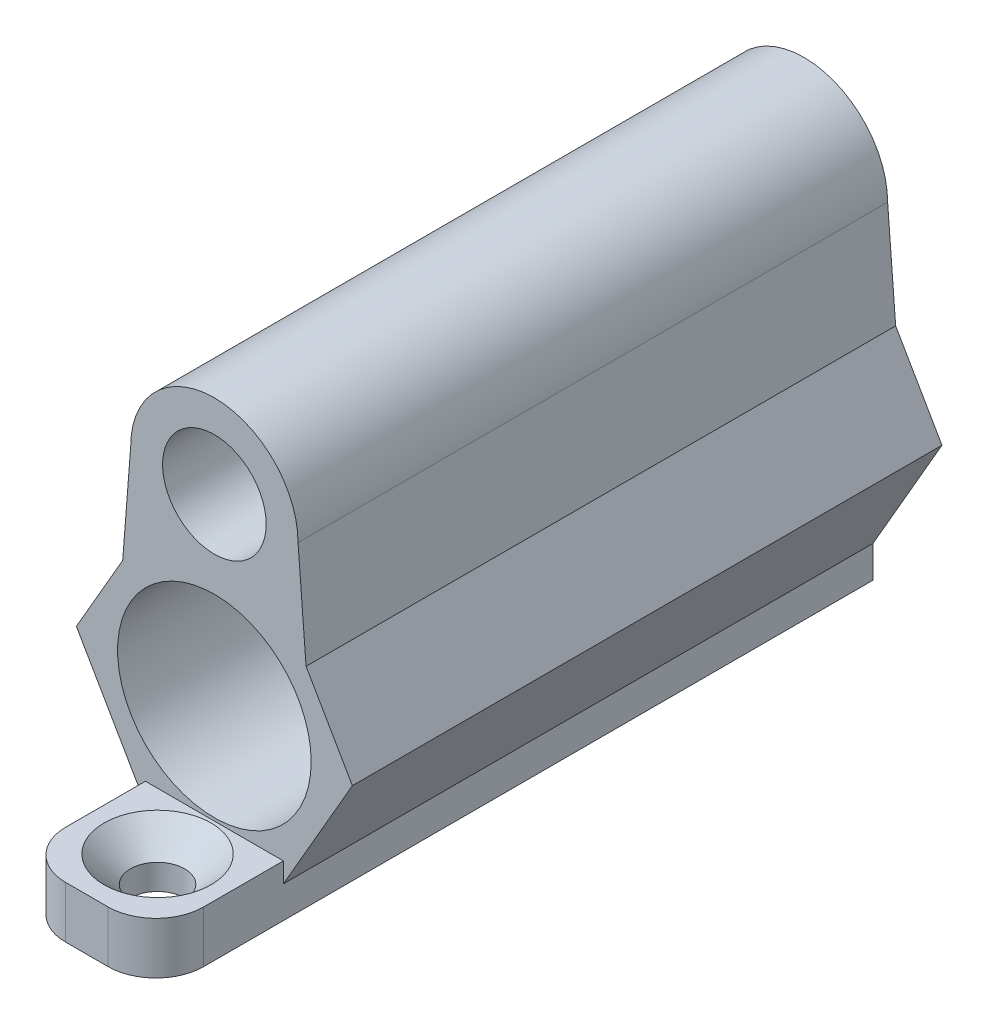
SolidWorks part; units mm, degrees
ref_plane "Front Plane" through (0, 0, 0) normal (0, 0, 1) x (1, 0, 0)
ref_plane "Top Plane" through (0, 0, 0) normal (0, 1, 0) x (1, 0, 0)
ref_plane "Right Plane" through (0, 0, 0) normal (1, 0, 0) x (0, 0, -1)
sketch "Sketch1" plane through (0, 0, 0) normal (0, 0, 1) x (1, 0, 0)
  line L0 (0, 0) -> (0, 43.6394) construction
  line L1 (0, 0) -> (58.8583, 0) construction
  line L2 (0, 0) -> (0, -43.088) construction
  line L3 (-3.9875, 4.3165) -> (-4.3301, 0)
  line L4 (8.6603, -7.5) -> (4.3301, 0)
  line L5 (4.3301, 0) -> (-4.3301, 0)
  line L6 (-4.3301, 0) -> (-8.6603, -7.5)
  line L7 (-8.6603, -7.5) -> (-4.3301, -15)
  line L8 (-4.3301, -15) -> (4.3301, -15)
  line L9 (4.3301, -15) -> (8.6603, -7.5)
  line L10 (3.9875, 4.3165) -> (4.3301, 0)
  circle A0 centre (0, -7.5) radius 7.5 construction
  circle A1 centre (0, 4) radius 4
  circle A2 centre (0, 4) radius 2.44
  circle A3 centre (0, -7.5) radius 2.44
  dimension "D1" = 15
  dimension "D2" = 8
  dimension "D3" = 4.88
  dimension "D4" = 4.88
extrude "Boss-Extrude2" add sketch "Sketch1" along normal blind 37 contours L8 L9 L4 L5 L6 L7 A3 | A1 L3 L5 | A1 A2 | A1 L5 L10
sketch "Sketch8" plane through (0, 0, 37) normal (0, 0, 1) x (1, 0, 0)
  circle A0 centre (0, 4) radius 3.25
  circle A1 centre (0, -7.5) radius 6.075
extrude "Cut-Extrude1" cut sketch "Sketch8" against normal blind 33
sketch "Sketch9" plane through (0, 0, 37) normal (0, 0, 1) x (1, 0, 0)
  line L1 (-4.3301, -15) -> (4.3301, -15)
  line L2 (-4.3301, -15) -> (-4.3301, -13.7541)
  line L3 (-4.3301, -13.7541) -> (4.3301, -13.7541)
  line L4 (4.3301, -15) -> (4.3301, -13.7541)
  dimension "D1" = 1.2459
sketch "Sketch15" plane through (0, 0, 37) normal (0, 0, 1) x (1, 0, 0)
  line L1 (-5.25, 4) -> (-5.7535, -2.4653)
  line L2 (-4.3301, 0) -> (-8.6603, -7.5) construction
  line L3 (5.25, 4) -> (5.7535, -2.4653)
  line L4 (8.6603, -7.5) -> (4.3301, 0) construction
  line L5 (5.7535, -2.4653) -> (2.1457, -0.7915)
  line L6 (-5.7535, -2.4653) -> (-1.8843, -0.9002)
  circle A0 centre (0, 4) radius 3.25
  circle A1 centre (0, 4) radius 5.25
  line M5 (8.6603, -7.5) -> (4.3301, 0)
  line M6 (4.3301, 0) -> (3.9875, 4.3165)
  arc M7 (3.9875, 4.3165) -> (-3.9875, 4.3165) centre (0, 4) ccw
  line M8 (-3.9875, 4.3165) -> (-4.3301, 0)
  line M9 (-4.3301, 0) -> (-8.6603, -7.5)
  dimension "D1" = 2
extrude "Boss-Extrude4" add sketch "Sketch15" against normal blind 37 contours A1 M8 M7 M6 | A1 L1 M9 M8 | A1 L3 M6 M5
sketch "Sketch18" plane through (0, -15, 0) normal (0, -1, 0) x (1, 0, 0)
  line L1 (-4.3301, 37) -> (4.3301, 37)
  line L2 (-4.3301, 37) -> (-4.3301, 0)
  line L3 (-4.3301, 0) -> (4.3301, 0)
  line L4 (4.3301, 37) -> (4.3301, 0)
extrude "Boss-Extrude5" add sketch "Sketch18" along normal blind 2
sketch "Sketch19" plane through (0, 0, 37) normal (0, 0, 1) x (1, 0, 0)
  line L1 (-4.3301, -13.7541) -> (4.3301, -13.7541)
  line L2 (-4.3301, -13.7541) -> (-4.3301, -17)
  line L3 (-4.3301, -17) -> (4.3301, -17)
  line L4 (4.3301, -13.7541) -> (4.3301, -17)
extrude "Boss-Extrude6" add sketch "Sketch19" along normal blind 8
fillet "Fillet4" radius 3 2 edges at (4.3301, -15.377, 45) (-4.3301, -15.377, 45)
sketch "Sketch20" plane through (0, -13.7541, 0) normal (0, 1, 0) x (1, 0, 0)
  circle A0 centre (0, -40.5654) radius 1.9128
hole_wizard "CSK for M3 Hex Socket Countersunk Cap Screw1" positions "3DSketch3" profile "Sketch21" countersink size "M3" standard "ISO" end condition through all
sketch3d "3DSketch3"
  point P1 (0, -13.7541, 40.5654)
sketch "Sketch21" plane through (0, -13.7541, 40.5654) normal (1, 0, 0) x (0, 0, 1)
  line L0 (0, 0) -> (0, 3.2459)
  line L1 (0, 3.2459) -> (1.7, 3.2459)
  line L2 (1.7, 3.2459) -> (1.7, 1.66)
  line L3 (1.7, 1.66) -> (3.36, 0)
  line L5 (3.36, 0) -> (0, 0)
  line L6 (-1.7, 1.66) -> (-3.36, 0) construction
  line L11 (0, -6.35) -> (0, 107.95) construction
  dimension "Thru Hole Dia." = 3.4
  dimension "Thru Hole Depth" = 3.2459
  dimension "Near C'Sink Dia." = 6.72
  dimension "Near C'Sink Angle" = 90
